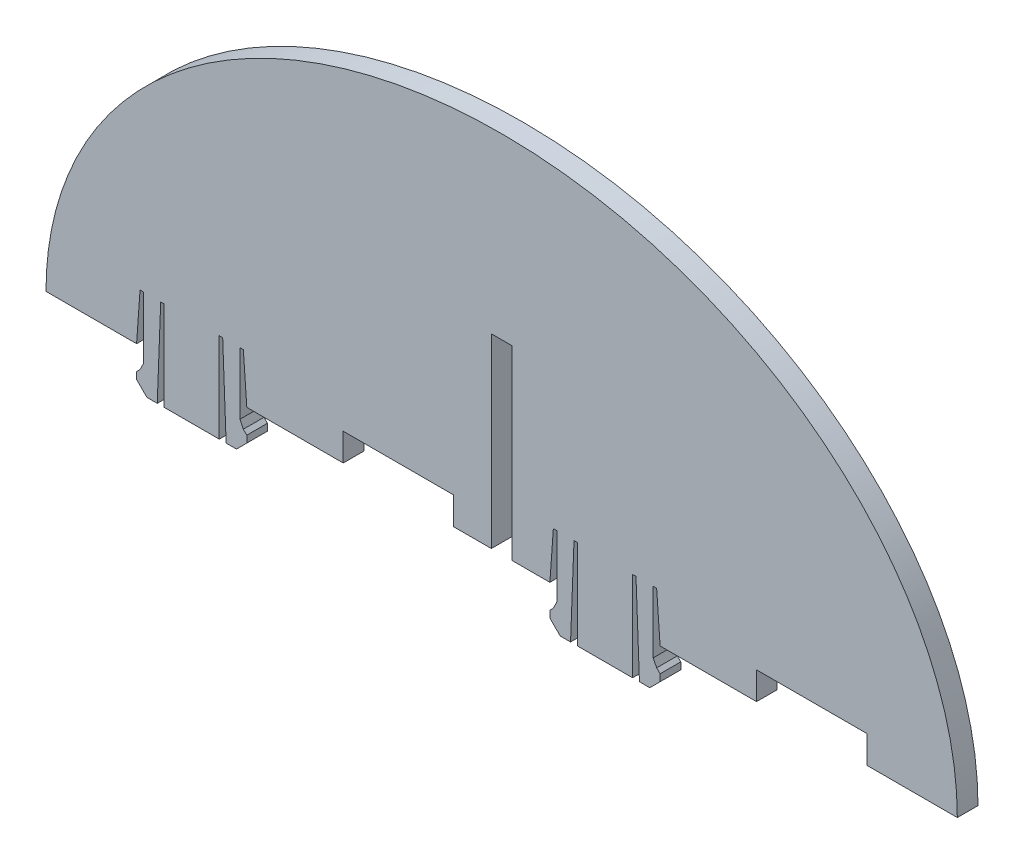
SolidWorks part; units mm, degrees
ref_plane "Front Plane" through (0, 0, 0) normal (0, 0, 1) x (1, 0, 0)
ref_plane "Top Plane" through (0, 0, 0) normal (0, 1, 0) x (1, 0, 0)
ref_plane "Right Plane" through (0, 0, 0) normal (1, 0, 0) x (0, 0, -1)
sketch "Sketch1" plane through (0, 0, 0) normal (0, 0, 1) x (1, 0, 0)
  line L0 (-53, 0) -> (-66.15, 0)
  line L1 (-37, 0) -> (-37.5, 7.0022)
  line L2 (-37.5, 7.0022) -> (-38, 7.0022)
  line L3 (-38, 7.0022) -> (-38, -1.9978)
  line L4 (-38, -1.9978) -> (-37.5, -2.9978)
  line L5 (-37.5, -2.9978) -> (-37, -3.4978)
  line L6 (-37, -3.4978) -> (-37, -4.4978)
  line L7 (-37, -4.4978) -> (-38.5, -5.9978)
  line L8 (-38.5, -5.9978) -> (-40, -5.9978)
  line L9 (-40, -5.9978) -> (-40.5, 7.0022)
  line L10 (-40.5, 7.0022) -> (-41, 7.0022)
  line L11 (-41, 7.0022) -> (-41, -5.9978)
  line L12 (-45, 0) -> (-45, -5.7386) construction
  line L13 (-49, 7.0022) -> (-49, -5.9978)
  line L14 (-49.5, 7.0022) -> (-49, 7.0022)
  line L15 (-50, -5.9978) -> (-49.5, 7.0022)
  line L16 (-51.5, -5.9978) -> (-50, -5.9978)
  line L17 (-53, -4.4978) -> (-51.5, -5.9978)
  line L18 (-53, -3.4978) -> (-53, -4.4978)
  line L19 (-52.5, -2.9978) -> (-53, -3.4978)
  line L20 (-52, -1.9978) -> (-52.5, -2.9978)
  line L21 (-52, 7.0022) -> (-52, -1.9978)
  line L22 (-52.5, 7.0022) -> (-52, 7.0022)
  line L23 (-53, 0) -> (-52.5, 7.0022)
  line L24 (-41, -5.9978) -> (-49, -5.9978)
  line L25 (23, 0) -> (22.5, 7.0022)
  line L26 (22.5, 7.0022) -> (22, 7.0022)
  line L27 (22, 7.0022) -> (22, -1.9978)
  line L28 (22, -1.9978) -> (22.5, -2.9978)
  line L29 (22.5, -2.9978) -> (23, -3.4978)
  line L30 (23, -3.4978) -> (23, -4.4978)
  line L31 (23, -4.4978) -> (21.5, -5.9978)
  line L32 (21.5, -5.9978) -> (20, -5.9978)
  line L33 (20, -5.9978) -> (19.5, 7.0022)
  line L34 (19.5, 7.0022) -> (19, 7.0022)
  line L35 (19, 7.0022) -> (19, -5.9978)
  line L36 (15, 0) -> (15, -5.7386) construction
  line L37 (11, 7.0022) -> (11, -5.9978)
  line L38 (10.5, 7.0022) -> (11, 7.0022)
  line L39 (10, -5.9978) -> (10.5, 7.0022)
  line L40 (8.5, -5.9978) -> (10, -5.9978)
  line L41 (7, -4.4978) -> (8.5, -5.9978)
  line L42 (7, -3.4978) -> (7, -4.4978)
  line L43 (7.5, -2.9978) -> (7, -3.4978)
  line L44 (8, -1.9978) -> (7.5, -2.9978)
  line L45 (8, 7.0022) -> (8, -1.9978)
  line L46 (7.5, 7.0022) -> (8, 7.0022)
  line L47 (7, 0) -> (7.5, 7.0022)
  line L48 (19, -5.9978) -> (11, -5.9978)
  line L49 (23, 0) -> (66.15, 0)
  line L50 (-37, 0) -> (7, 0)
  ellipse E0 centre (0, 0) end of major axis (-66.15, 0) minor radius 52.91 (0, 52.91) -> (66.15, 0) cw
  ellipse E1 centre (0, 0) end of major axis (66.15, 0) minor radius 52.91 (0, 52.91) -> (-66.15, 0) ccw
  point P4 (0, 0)
  point P20 (23, 0)
  point P22 (-37, 0)
  dimension "D3" = 66.15
  dimension "D4" = 0.5
  dimension "D5" = 9
  dimension "D6" = 0.5
  dimension "D7" = 1
  dimension "D8" = 0.5
  dimension "D9" = 0.5
  dimension "D10" = 1
  dimension "D11" = 1.5
  dimension "D12" = 1.5
  dimension "D13" = 0.5
  dimension "D14" = 0.5
  dimension "D15" = 13
  dimension "D16" = 7.0022
  dimension "D17" = 0.5
  dimension "D18" = 1.5
  dimension "D19" = 13
  dimension "D20" = 8
  dimension "D21" = 52.91
  dimension "D22" = 43.15
  dimension "D23" = 0.5
  dimension "D24" = 9
  dimension "D25" = 0.5
  dimension "D26" = 1
  dimension "D27" = 0.5
  dimension "D28" = 0.5
  dimension "D29" = 1
  dimension "D30" = 1.5
  dimension "D31" = 1.5
  dimension "D32" = 0.5
  dimension "D33" = 0.5
  dimension "D34" = 13
  dimension "D35" = 7.0022
  dimension "D36" = 0.5
  dimension "D37" = 1.5
  dimension "D38" = 13
  dimension "D39" = 8
  dimension "D40" = 13.15
  dimension "D41" = 44
  dimension "D42" = 66.15
  dimension "D43" = 52.91
  dimension "D44" = 52.91
extrude "Boss-Extrude1" add sketch "Sketch1" along normal blind 3
sketch "Sketch2" plane through (0, 0, 3) normal (0, 0, 1) x (1, 0, 0)
  line L0 (-1.5, 0) -> (-1.5, 27)
  line L1 (-37, 0) -> (7, 0) construction
  line L2 (-1.5, 27) -> (1.5, 27)
  line L3 (1.5, 27) -> (1.5, 0)
  dimension "D1" = 27
  dimension "D2" = 3
  dimension "D3" = 1.5
extrude "Cut-Extrude1" cut sketch "Sketch2" against normal blind 3 and the other way through all flip side to cut
sketch "Sketch3" plane through (0, 0, 3) normal (0, 0, 1) x (1, 0, 0)
  line L0 (-23, 0) -> (-23, 4)
  line L2 (-37, 0) -> (-1.5, 0) construction
  line L3 (-23, 4) -> (-7, 4)
  line L4 (-7, 4) -> (-7, 0)
  dimension "D1" = 16
  dimension "D2" = 4
  dimension "D3" = 7
extrude "Cut-Extrude2" cut sketch "Sketch3" against normal blind 3 and the other way through all flip side to cut
sketch "Sketch4" plane through (0, 0, 3) normal (0, 0, 1) x (1, 0, 0)
  line L0 (37, 0) -> (37, 4)
  line L1 (23, 0) -> (66.15, 0) construction
  line L2 (37, 4) -> (53, 4)
  line L3 (53, 4) -> (53, 0)
  dimension "D1" = 16
  dimension "D2" = 4
  dimension "D3" = 13.15
extrude "Cut-Extrude3" cut sketch "Sketch4" against normal blind 3 and the other way through all flip side to cut
sketch "Sketch5" plane through (0, 0, 3) normal (0, 0, 1) x (1, 0, 0)
  text T0 "HY3b" font "Century Gothic" height in points 20
  dimension "D1" = 24.5593
  dimension "D2" = 7.9866
